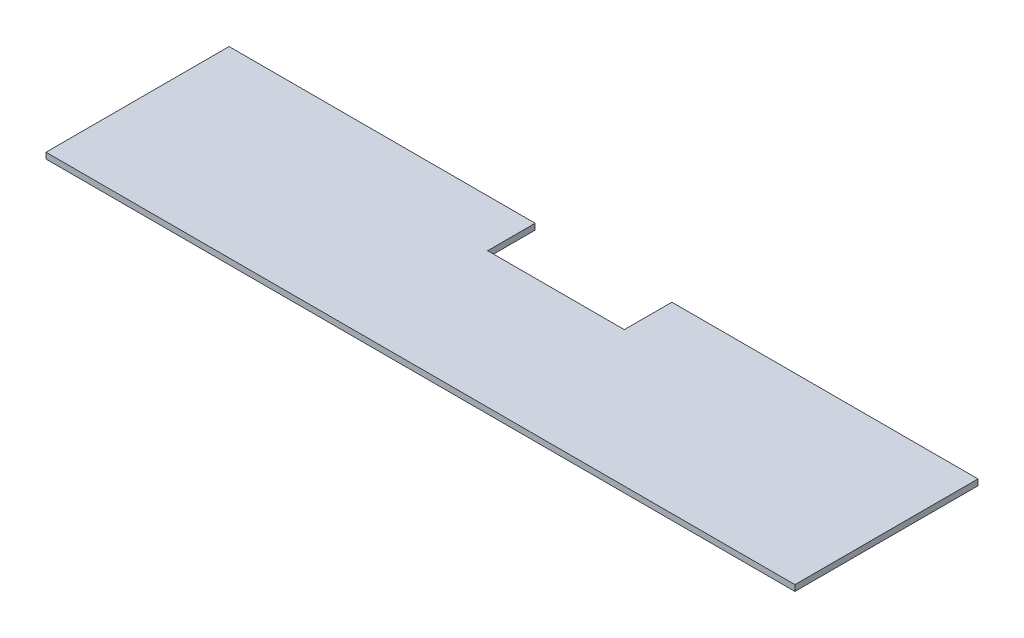
SolidWorks part; units mm, degrees
ref_plane "Front Plane" through (0, 0, 0) normal (0, 0, 1) x (1, 0, 0)
ref_plane "Top Plane" through (0, 0, 0) normal (0, 1, 0) x (1, 0, 0)
ref_plane "Right Plane" through (0, 0, 0) normal (1, 0, 0) x (0, 0, -1)
sketch "Sketch5" plane through (0, 0, 0) normal (0, 1, 0) x (1, 0, 0)
  line L1 (0, 0) -> (381, 0)
  line L2 (0, 0) -> (0, 195.58)
  line L3 (0, 195.58) -> (381, 195.58)
  line L4 (381, 0) -> (381, 195.58)
  dimension "D1" = 381
  dimension "D2" = 195.58
extrude "Boss-Extrude2" add sketch "Sketch5" along normal blind 6.35
sketch "Sketch6" plane through (0, 0, 0) normal (0, 1, 0) x (1, 0, 0)
  line L1 (381, 0) -> (590.55, 0)
  line L2 (381, 0) -> (381, 195.58)
  line L3 (381, 195.58) -> (590.55, 195.58)
  line L4 (590.55, 0) -> (590.55, 195.58)
  dimension "D1" = 195.58
  dimension "D2" = 209.55
extrude "Boss-Extrude3" add sketch "Sketch6" along normal blind 6.35
sketch "Sketch7" plane through (0, 0, 0) normal (0, 1, 0) x (1, 0, 0)
  line L1 (0, 0) -> (-209.55, 0)
  line L2 (0, 0) -> (0, 195.58)
  line L3 (0, 195.58) -> (-209.55, 195.58)
  line L4 (-209.55, 0) -> (-209.55, 195.58)
  dimension "D1" = 209.55
  dimension "D2" = 195.58
extrude "Boss-Extrude4" add sketch "Sketch7" along normal blind 6.35
sketch "Sketch8" plane through (0, 6.35, 0) normal (0, 1, 0) x (1, 0, 0)
  line L0 (412.75, 195.58) -> (412.75, 0)
  line L1 (590.55, 195.58) -> (-209.55, 195.58) construction
  line L2 (-209.55, 0) -> (590.55, 0) construction
  line L3 (590.55, 0) -> (590.55, 195.58) construction
  line L4 (215.9, 195.58) -> (215.9, 0)
  line L5 (190.5, 195.58) -> (190.5, 0) construction
  line L6 (-31.75, 195.58) -> (-31.75, 0)
  line L7 (165.1, 195.58) -> (165.1, 0)
  dimension "D1" = 177.8
  dimension "D2" = 196.85
sketch "Sketch9" plane through (0, 6.35, 0) normal (0, 1, 0) x (1, 0, 0)
  line L0 (590.55, 195.58) -> (-209.55, 195.58) construction
  line L1 (117.475, 195.58) -> (263.525, 195.58)
  line L2 (117.475, 195.58) -> (117.475, 144.78)
  line L3 (117.475, 144.78) -> (263.525, 144.78)
  line L4 (263.525, 195.58) -> (263.525, 144.78)
  line L5 (215.9, 195.58) -> (215.9, 0) construction
  line L6 (165.1, 195.58) -> (165.1, 0) construction
  dimension "D1" = 50.8
  dimension "D2" = 47.625
  dimension "D3" = 47.625
extrude "Cut-Extrude1" cut sketch "Sketch9" against normal through all
